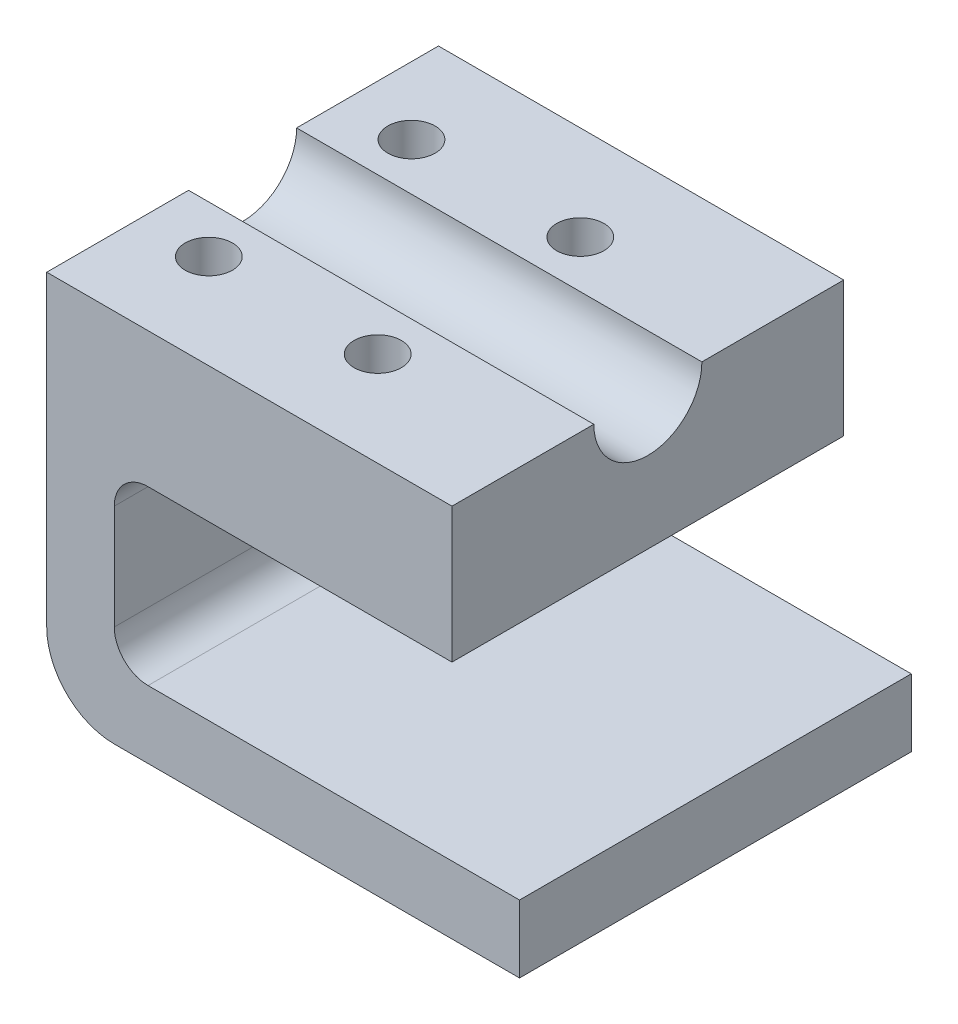
SolidWorks part; units mm, degrees
ref_plane "Front Plane" through (0, 0, 0) normal (0, 0, 1) x (1, 0, 0)
ref_plane "Top Plane" through (0, 0, 0) normal (0, 1, 0) x (1, 0, 0)
ref_plane "Right Plane" through (0, 0, 0) normal (1, 0, 0) x (0, 0, -1)
sketch "Sketch1" plane through (0, 0, 0) normal (0, 0, 1) x (1, 0, 0)
  line L2 (0, 0) -> (0, 25.5)
  line L5 (0, 0) -> (60, 0)
  line L7 (0, -10) -> (60, -10)
  line L8 (60, 0) -> (60, -10)
  line L9 (0, 25.5) -> (50, 25.5)
  line L10 (-10, 0) -> (-10, 45.5)
  line L11 (-10, 45.5) -> (50, 45.5)
  line L12 (50, 25.5) -> (50, 45.5)
  arc A0 (-10, 0) -> (0, -10) centre (0, 0) ccw
  dimension "D5" = 10
  dimension "D1" = 25.5
  dimension "D2" = 45.5
  dimension "D3" = 60
  dimension "D4" = 10
  dimension "D6" = 60
  dimension "D7" = 20
extrude "Boss-Extrude1" add sketch "Sketch1" along normal blind 58
sketch "Sketch2" plane through (-10, 0, 0) normal (-1, 0, 0) x (0, 0, 1)
  line L0 (58, 45.5) -> (0, 45.5) construction
  circle A0 centre (29, 45.5) radius 8
  dimension "D1" = 16
extrude "Cut-Extrude1" cut sketch "Sketch2" against normal blind 60
sketch "Sketch3" plane through (0, 45.5, 0) normal (0, 1, 0) x (1, 0, 0)
  line L0 (-10, -21) -> (-10, 0) construction
  line L1 (-10, -21) -> (-10, -37) construction
  circle A0 centre (0, -14) radius 3.5
  circle A1 centre (0, -44) radius 3.5
  circle A2 centre (25, -14) radius 3.5
  circle A3 centre (25, -44) radius 3.5
  point P6 (-10, -29)
  dimension "D3" = 7
  dimension "D5" = 7
  dimension "D1" = 10
  dimension "D2" = 15
  dimension "D4" = 30
  dimension "D6" = 25
extrude "Cut-Extrude2" cut sketch "Sketch3" against normal blind 18
fillet "Fillet1" radius 5 2 edges at (0, 0, 29) (0, 25.5, 29)
